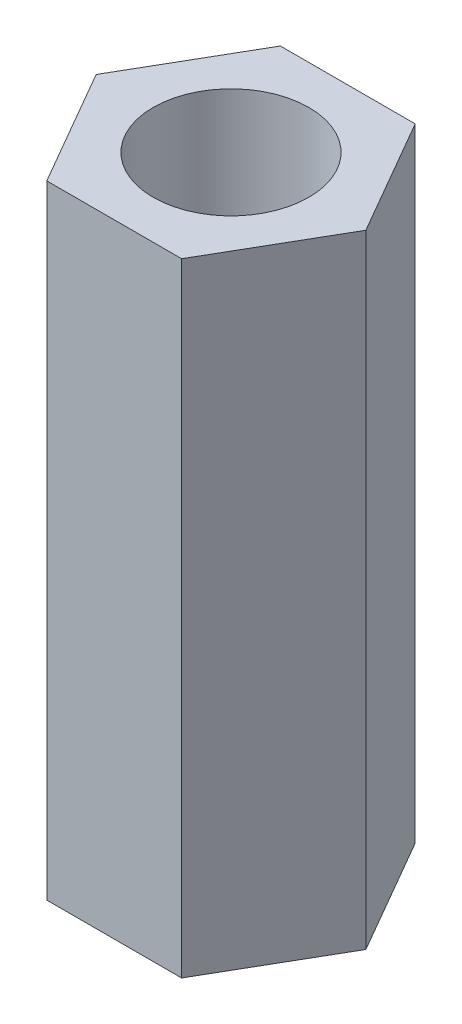
SolidWorks part; units mm, degrees
ref_plane "Front Plane" through (0, 0, 0) normal (0, 0, 1) x (1, 0, 0)
ref_plane "Top Plane" through (0, 0, 0) normal (0, 1, 0) x (1, 0, 0)
ref_plane "Right Plane" through (0, 0, 0) normal (1, 0, 0) x (0, 0, -1)
sketch "Sketch2" plane through (0, 0, 0) normal (0, 1, 0) x (1, 0, 0)
  line L1 (-1.299, 2.25) -> (-2.5981, 0)
  line L2 (-2.5981, 0) -> (-1.299, -2.25)
  line L3 (-1.299, -2.25) -> (1.299, -2.25)
  line L4 (1.299, -2.25) -> (2.5981, 0)
  line L5 (2.5981, 0) -> (1.299, 2.25)
  line L6 (1.299, 2.25) -> (-1.299, 2.25)
  circle A0 centre (0, 0) radius 2.25 construction
  dimension "D1" = 4.5
extrude "Boss-Extrude1" add sketch "Sketch2" along normal blind 12
sketch "Sketch3" plane through (0, 12, 0) normal (0, 1, 0) x (1, 0, 0)
  circle A0 centre (0, 0) radius 1.5
  dimension "D1" = 3
extrude "Cut-Extrude1" cut sketch "Sketch3" against normal through all
